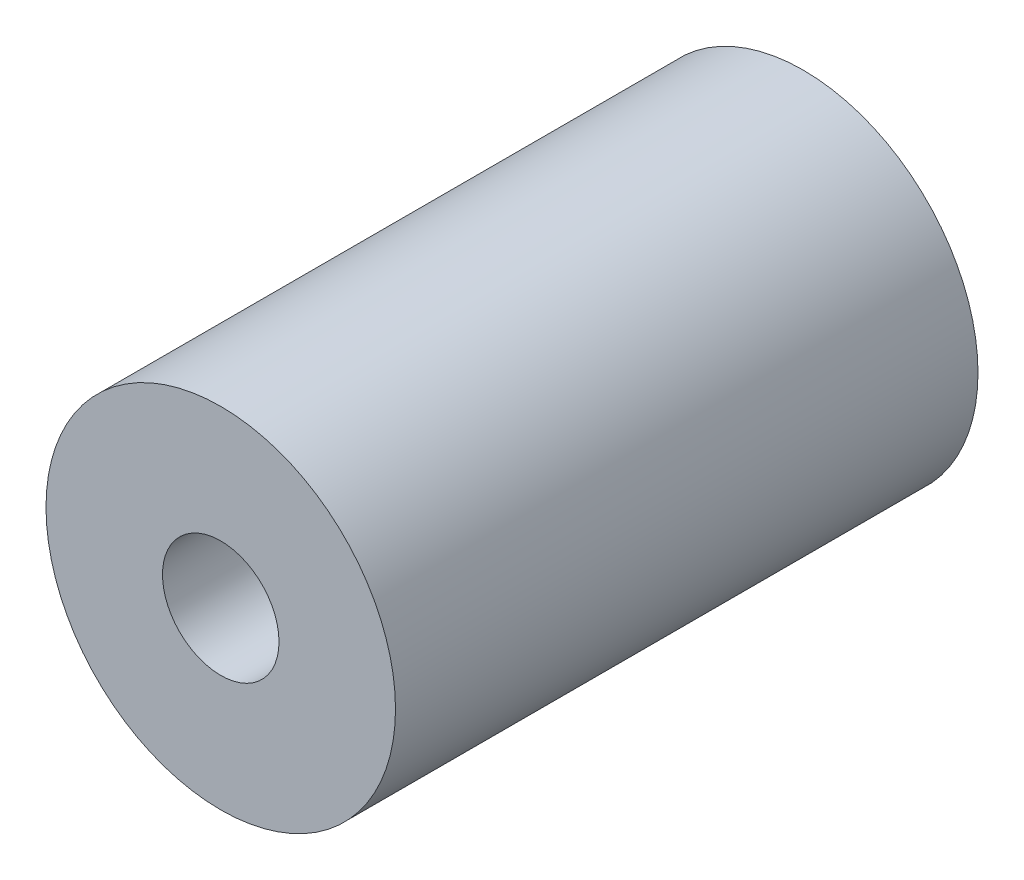
SolidWorks part; units mm, degrees
ref_plane "Front Plane" through (0, 0, 0) normal (0, 0, 1) x (1, 0, 0)
ref_plane "Top Plane" through (0, 0, 0) normal (0, 1, 0) x (1, 0, 0)
ref_plane "Right Plane" through (0, 0, 0) normal (1, 0, 0) x (0, 0, -1)
sketch "Sketch1" plane through (0, 0, 0) normal (0, 0, 1) x (1, 0, 0)
  circle A0 centre (0, 0) radius 3
  dimension "D1" = 6
extrude "Extrude-Thin1" add sketch "Sketch1" along normal blind 10 thin thin type one direction reverse wall 2
